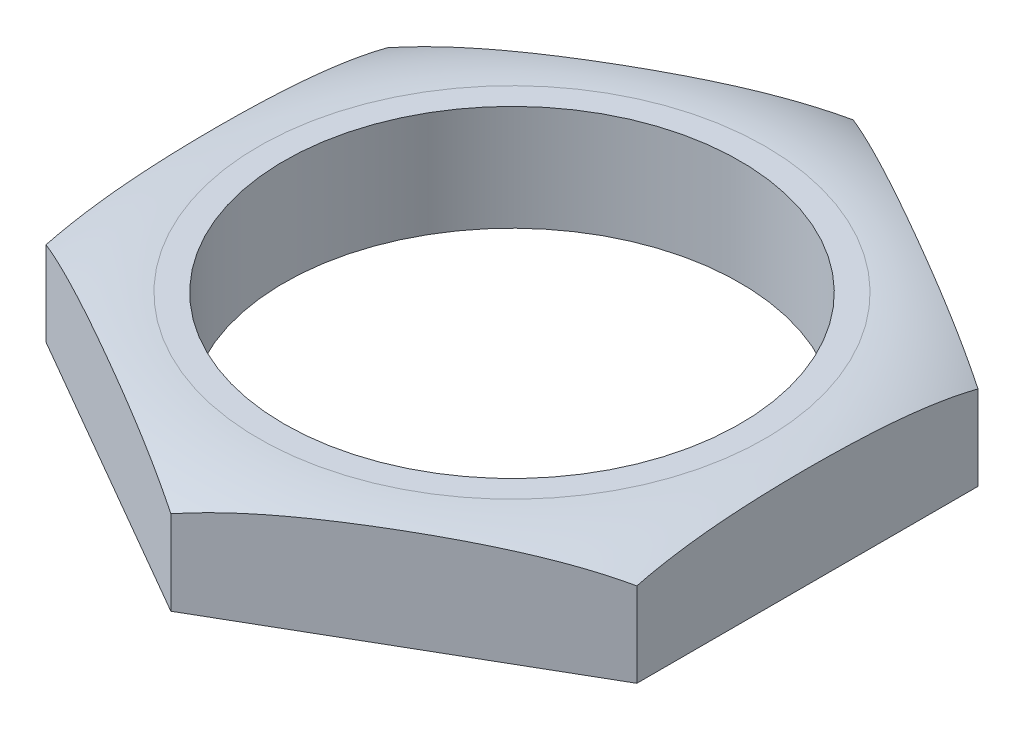
SolidWorks part; units mm, degrees
material "Хромированная нержавеющая сталь"
ref_plane "Спереди" through (0, 0, 0) normal (0, 0, 1) x (1, 0, 0)
ref_plane "Сверху" through (0, 0, 0) normal (0, 1, 0) x (1, 0, 0)
ref_plane "Справа" through (0, 0, 0) normal (1, 0, 0) x (0, 0, -1)
sketch "Эскиз1" plane through (0, 0, 0) normal (0, 1, 0) x (1, 0, 0)
  line L1 (0, -8.0829) -> (7, -4.0415)
  line L2 (7, -4.0415) -> (7, 4.0415)
  line L3 (7, 4.0415) -> (0, 8.0829)
  line L4 (0, 8.0829) -> (-7, 4.0415)
  line L5 (-7, 4.0415) -> (-7, -4.0415)
  line L6 (-7, -4.0415) -> (0, -8.0829)
  circle A0 centre (0, 0) radius 7 construction
  dimension "D1" = 14
extrude "Бобышка-Вытянуть1" add sketch "Эскиз1" along normal blind 2.5
sketch "Эскиз2" plane through (0, 0, 0) normal (1, 0, 0) x (0, 0, -1)
  line L0 (0, 0) -> (0, 2.5) construction
  line L1 (-4.0415, 2.5) -> (4.0415, 2.5) construction
  line L2 (-8.0829, 2.5) -> (-8.0829, 2)
  line L4 (-8.0829, 2.5) -> (-8.0829, 0) construction
  line L6 (-8.0829, 2.5) -> (-6, 2.5)
  line L8 (-4.0415, 2.5) -> (-8.0829, 2.5) construction
  arc A0 (-6, 2.5) -> (-8.0829, 2) centre (-6, -2.0885) ccw
  dimension "D1" = 0.5
revolve "Вырез-Повернуть1" cut sketch "Эскиз2" angle 360 about L0
sketch "Эскиз8" plane through (0, 2.5, 0) normal (0, 1, 0) x (1, 0, 0)
  point P0 (0, 0)
hole_wizard "Отверстие обработанное метчиком M12x1.252" positions "Трехмерный эскиз6" profile "Эскиз10" tap size "M12x1.25" standard "Ansi Metric" end condition through all
sketch3d "Трехмерный эскиз6"
  point P0 (0, 2.5, 0)
sketch "Эскиз10" plane through (0, 2.5, 0) normal (1, 0, 0) x (0, 0, 1)
  line L0 (0, 0) -> (0, 2.5)
  line L1 (0, 2.5) -> (5.4, 2.5)
  line L2 (5.4, 2.5) -> (5.4, 0)
  line L5 (5.4, 0) -> (0, 0)
  line L11 (0, -6.35) -> (0, 107.95) construction
  dimension "Диаметр проходного сверла" = 10.8
  dimension "Глубина проходного сверла" = 2.5
cosmetic thread "Отверстие резьбы2" parameters "D2"=12
